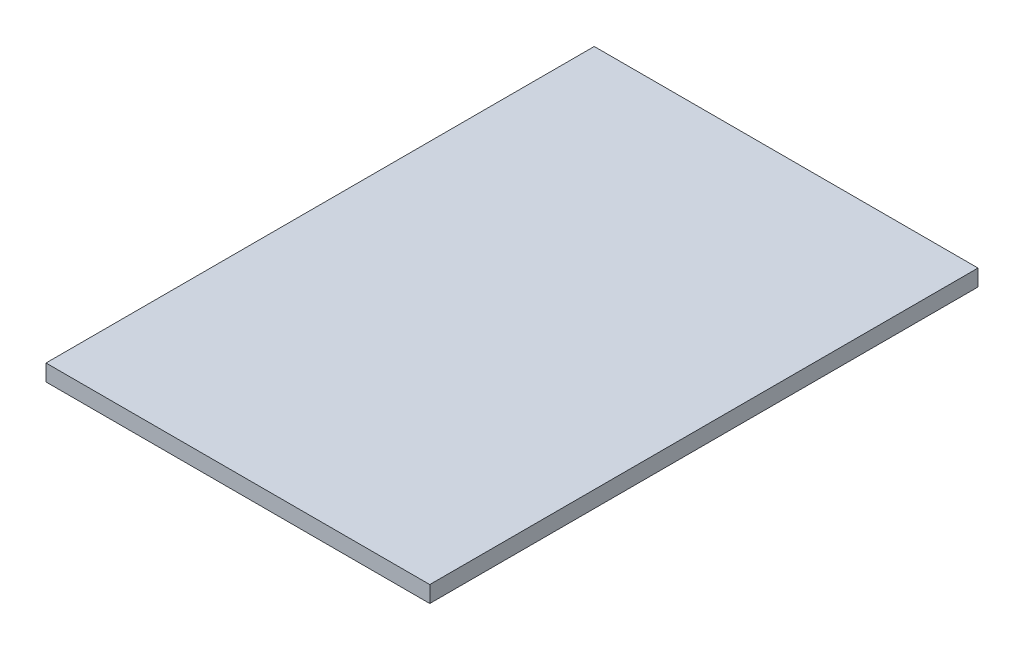
SolidWorks part; units mm, degrees
ref_plane "Alzado" through (0, 0, 0) normal (0, 0, 1) x (1, 0, 0)
ref_plane "Planta" through (0, 0, 0) normal (0, 1, 0) x (1, 0, 0)
ref_plane "Vista lateral" through (0, 0, 0) normal (1, 0, 0) x (0, 0, -1)
sketch "Croquis1" plane through (0, 0, 0) normal (0, 1, 0) x (1, 0, 0)
  line L1 (-350, 500) -> (350, 500)
  line L2 (-350, 500) -> (-350, -500)
  line L3 (-350, -500) -> (350, -500)
  line L4 (350, 500) -> (350, -500)
  line L5 (-350, 500) -> (350, -500) construction
  line L6 (-350, -500) -> (350, 500) construction
  point P0 (0, 0)
  dimension "D1" = 700
  dimension "D2" = 1000
extrude "Saliente-Extruir1" add sketch "Croquis1" along normal blind 20
sketch "Croquis2" plane through (0, 0, 0) normal (0, -1, 0) x (-1, 0, 0)
  line L1 (350, -500) -> (-350, -500)
  line L2 (350, -500) -> (350, 500)
  line L3 (350, 500) -> (-350, 500)
  line L4 (-350, -500) -> (-350, 500)
  line L5 (350, -500) -> (-350, 500) construction
  line L6 (350, 500) -> (-350, -500) construction
  point P0 (0, 0)
extrude "Saliente-Extruir2" add sketch "Croquis2" along normal blind 10
